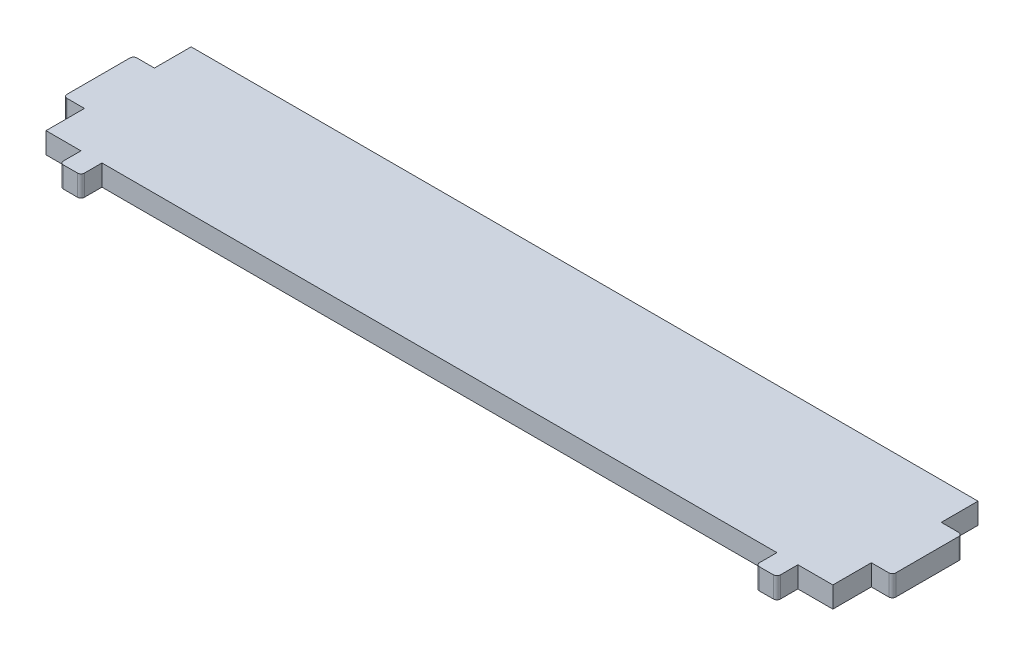
SolidWorks part; units mm, degrees
ref_plane "Спереди" through (0, 0, 0) normal (0, 0, 1) x (1, 0, 0)
ref_plane "Сверху" through (0, 0, 0) normal (0, 1, 0) x (1, 0, 0)
ref_plane "Справа" through (0, 0, 0) normal (1, 0, 0) x (0, 0, -1)
sketch "Эскиз1" plane through (0, 0, 0) normal (0, 1, 0) x (1, 0, 0)
  line L0 (0, -20.75) -> (0, 21.8864) construction
  line L1 (-56.25, -20.75) -> (56.25, -20.75)
  line L2 (56.25, -20.75) -> (56.25, -15.25)
  line L5 (56.25, -15.25) -> (59.25, -15.25)
  line L6 (59.25, -15.25) -> (59.25, -5.25)
  line L7 (59.25, -5.25) -> (56.25, -5.25)
  line L8 (56.25, -5.25) -> (56.25, 0)
  line L9 (56.25, 0) -> (-56.25, 0)
  line L10 (-56.25, -5.25) -> (-56.25, 0)
  line L11 (-59.25, -5.25) -> (-56.25, -5.25)
  line L12 (-59.25, -15.25) -> (-59.25, -5.25)
  line L13 (-56.25, -15.25) -> (-59.25, -15.25)
  line L16 (-56.25, -20.75) -> (-56.25, -15.25)
  line L17 (-48.25, -20.75) -> (-51.25, -23.75) construction
  line L18 (48.25, -23.75) -> (51.25, -23.75)
  line L19 (48.25, -23.75) -> (48.25, -20.75)
  line L20 (48.25, -20.75) -> (51.25, -20.75)
  line L21 (51.25, -23.75) -> (51.25, -20.75)
  line L22 (48.25, -23.75) -> (51.25, -20.75) construction
  line L23 (48.25, -20.75) -> (51.25, -23.75) construction
  line L24 (-48.25, -23.75) -> (-51.25, -20.75) construction
  line L25 (-51.25, -23.75) -> (-51.25, -20.75)
  line L26 (-48.25, -20.75) -> (-51.25, -20.75)
  line L27 (-48.25, -23.75) -> (-48.25, -20.75)
  line L28 (-48.25, -23.75) -> (-51.25, -23.75)
  point P3 (49.75, -22.25)
  point P13 (57.75, -5.25)
  point P14 (50, -9.6)
  point P18 (0, 0)
  point P25 (-50, -9.6)
  point P28 (-49.75, -22.25)
  dimension "D5" = 3
  dimension "D1" = 3
  dimension "D2" = 10
  dimension "D3" = 6.25
  dimension "D4" = 20.75
  dimension "D6" = 5.25
  dimension "D7" = 100
  dimension "D8" = 5
  dimension "D9" = 9.6
extrude "Бобышка-Вытянуть1" add sketch "Эскиз1" along normal blind 3
fillet "Скругление1" radius 0.5 8 edges at (-59.25, 1.5, 5.25) (-59.25, 1.5, 15.25) (59.25, 1.5, 5.25) (59.25, 1.5, 15.25) (-51.25, 1.5, 23.75) (-48.25, 1.5, 23.75) (48.25, 1.5, 23.75) (51.25, 1.5, 23.75)
